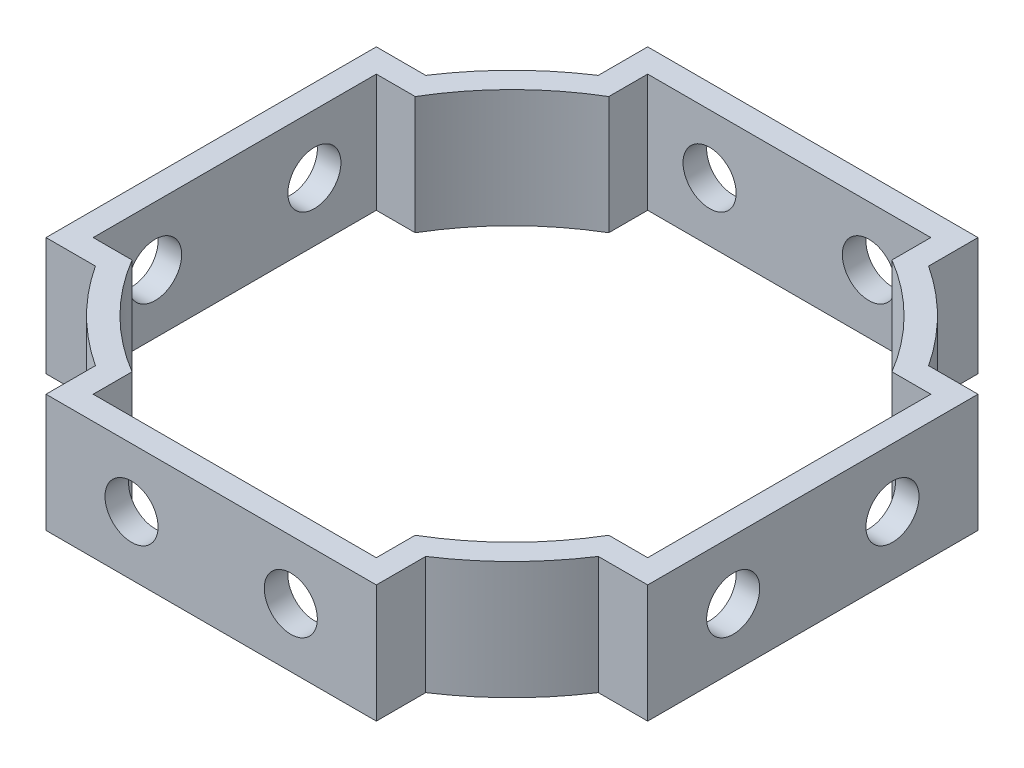
SolidWorks part; units mm, degrees
ref_plane "前视基准面" through (0, 0, 0) normal (0, 0, 1) x (1, 0, 0)
ref_plane "上视基准面" through (0, 0, 0) normal (0, 1, 0) x (1, 0, 0)
ref_plane "右视基准面" through (0, 0, 0) normal (1, 0, 0) x (0, 0, -1)
sketch "草图1" plane through (0, 0, 0) normal (0, 1, 0) x (1, 0, 0)
  circle A0 centre (0, 0) radius 23.5
  circle A1 centre (0, 0) radius 25.5
  dimension "D1" = 47
  dimension "D2" = 51
extrude "凸台-拉伸1" add sketch "草图1" along normal blind 10
sketch "草图2" plane through (0, 10, 0) normal (0, 1, 0) x (1, 0, 0)
  line L0 (0, 0.3004) -> (0, 25.5) construction
  line L1 (-14, 25.5) -> (14, 25.5)
  line L2 (14, 25.5) -> (14, 20.2052)
  line L3 (-14, 20.2052) -> (-14, 25.5)
  line L4 (20.2052, 14) -> (25.5, 14)
  line L5 (25.5, 14) -> (25.5, -14)
  line L6 (25.5, -14) -> (20.2052, -14)
  line L7 (14, -20.2052) -> (14, -25.5)
  line L8 (14, -25.5) -> (-14, -25.5)
  line L9 (-14, -25.5) -> (-14, -20.2052)
  line L10 (-20.2052, -14) -> (-25.5, -14)
  line L11 (-25.5, -14) -> (-25.5, 14)
  line L12 (-25.5, 14) -> (-20.2052, 14)
  arc A0 (14, 20.2052) -> (-14, 20.2052) centre (0, 0) ccw
  circle A1 centre (0, 0) radius 25.5 construction
  arc A2 (20.2052, -14) -> (20.2052, 14) centre (0, 0) ccw
  arc A3 (-14, -20.2052) -> (14, -20.2052) centre (0, 0) ccw
  arc A4 (-20.2052, 14) -> (-20.2052, -14) centre (0, 0) ccw
  point P25 (0, 0)
  dimension "D1" = 14
  dimension "D2" = 4
extrude "凸台-拉伸2" add sketch "草图2" against normal blind 10
sketch "草图3" plane through (0, 0, 25.5) normal (0, 0, 1) x (1, 0, 0)
  line L0 (0, 10) -> (0, 0) construction
  line L1 (-14, 10) -> (14, 10) construction
  circle A0 centre (-6.75, 5) radius 2.25
  circle A1 centre (6.75, 5) radius 2.25
  dimension "D1" = 5
  dimension "D2" = 6.75
extrude "切除-拉伸1" cut sketch "草图3" against normal through all
sketch "草图4" plane through (-25.5, 0, 0) normal (-1, 0, 0) x (0, 0, 1)
  line L0 (0, 10) -> (0, 0) construction
  line L1 (-14, 10) -> (14, 10) construction
  line L2 (-14, 0) -> (14, 0) construction
  circle A0 centre (-6.75, 5) radius 2.25
  circle A1 centre (6.75, 5) radius 2.25
  dimension "D1" = 5
  dimension "D2" = 6.75
extrude "切除-拉伸2" cut sketch "草图4" against normal through all
sketch "草图7" plane through (0, 10, 0) normal (0, 1, 0) x (1, 0, 0)
  line L0 (0, 25.5) -> (0, 0) construction
  line L1 (14, 25.5) -> (-14, 25.5) construction
  line L2 (-12, 23.5) -> (12, 23.5)
  line L3 (12, 23.5) -> (12, 19.7684)
  line L4 (12, 19.7684) -> (-12, 19.7684)
  line L5 (-12, 23.5) -> (-12, 19.7684)
  line L6 (23.5, 12) -> (19.7684, 12)
  line L7 (19.7684, -12) -> (19.7684, 12)
  line L8 (23.5, -12) -> (19.7684, -12)
  line L9 (23.5, 12) -> (23.5, -12)
  line L10 (12, -23.5) -> (12, -19.7684)
  line L11 (-12, -19.7684) -> (12, -19.7684)
  line L12 (-12, -23.5) -> (-12, -19.7684)
  line L13 (12, -23.5) -> (-12, -23.5)
  line L14 (-23.5, -12) -> (-19.7684, -12)
  line L15 (-19.7684, 12) -> (-19.7684, -12)
  line L16 (-23.5, 12) -> (-19.7684, 12)
  line L17 (-23.5, -12) -> (-23.5, 12)
  point P9 (0, 23.5)
  point P11 (0, 19.7684)
  point P26 (0, 0)
  dimension "D1" = 2
  dimension "D2" = 12
  dimension "D3" = 4
extrude "切除-拉伸4" cut sketch "草图7" against normal through all
